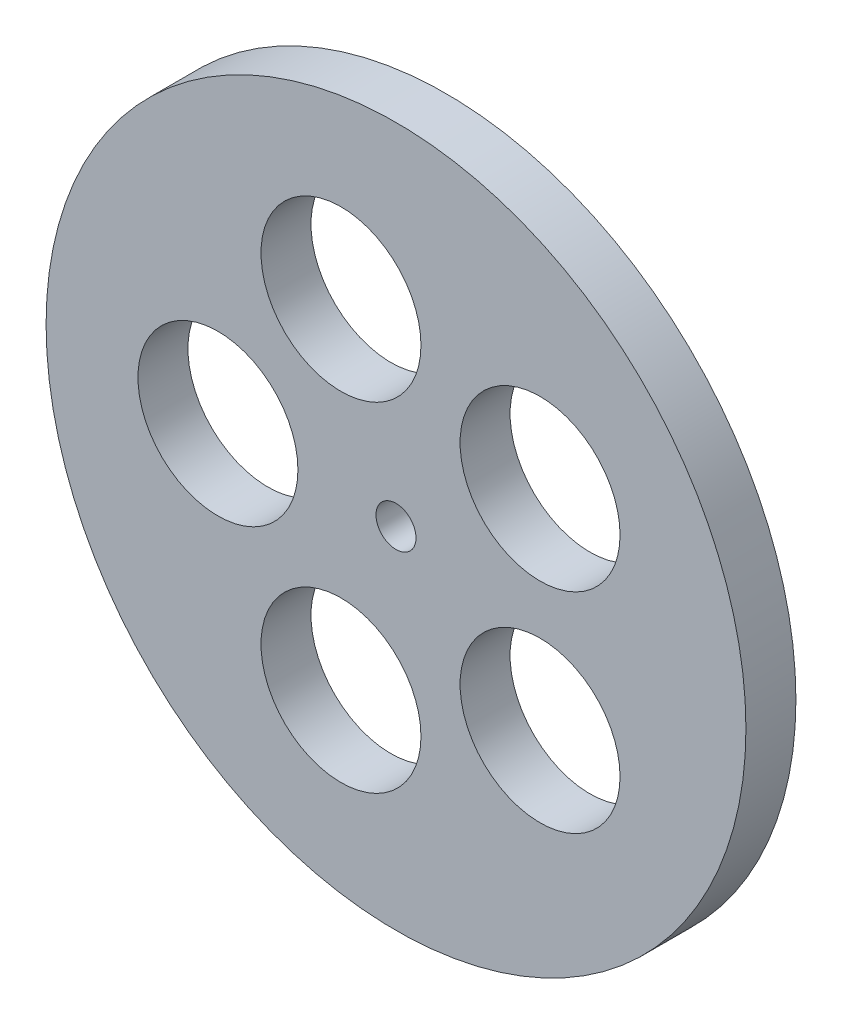
SolidWorks part; units mm, degrees
ref_plane "Plan de face" through (0, 0, 0) normal (0, 0, 1) x (1, 0, 0)
ref_plane "Plan de dessus" through (0, 0, 0) normal (0, 1, 0) x (1, 0, 0)
ref_plane "Plan de droite" through (0, 0, 0) normal (1, 0, 0) x (0, 0, -1)
sketch "Esquisse1" plane through (0, 0, 0) normal (0, 0, 1) x (1, 0, 0)
  circle A0 centre (0, 0) radius 35
  circle A1 centre (0, 0) radius 2
extrude "circonference" add sketch "Esquisse1" along normal blind 5
sketch "Esquisse2" plane through (0, 0, 5) normal (0, 0, 1) x (1, 0, 0)
  circle A0 centre (-17.8103, 0) radius 8
  circle A1 centre (-5.5037, 16.9386) radius 8
  circle A2 centre (14.4088, 10.4686) radius 8
  circle A3 centre (14.4088, -10.4686) radius 8
  circle A4 centre (-5.5037, -16.9386) radius 8
  point P13 (0, 0)
  dimension "D1" = 5
extrude "Enlèv. mat.-Extru.1" cut sketch "Esquisse2" against normal through all
